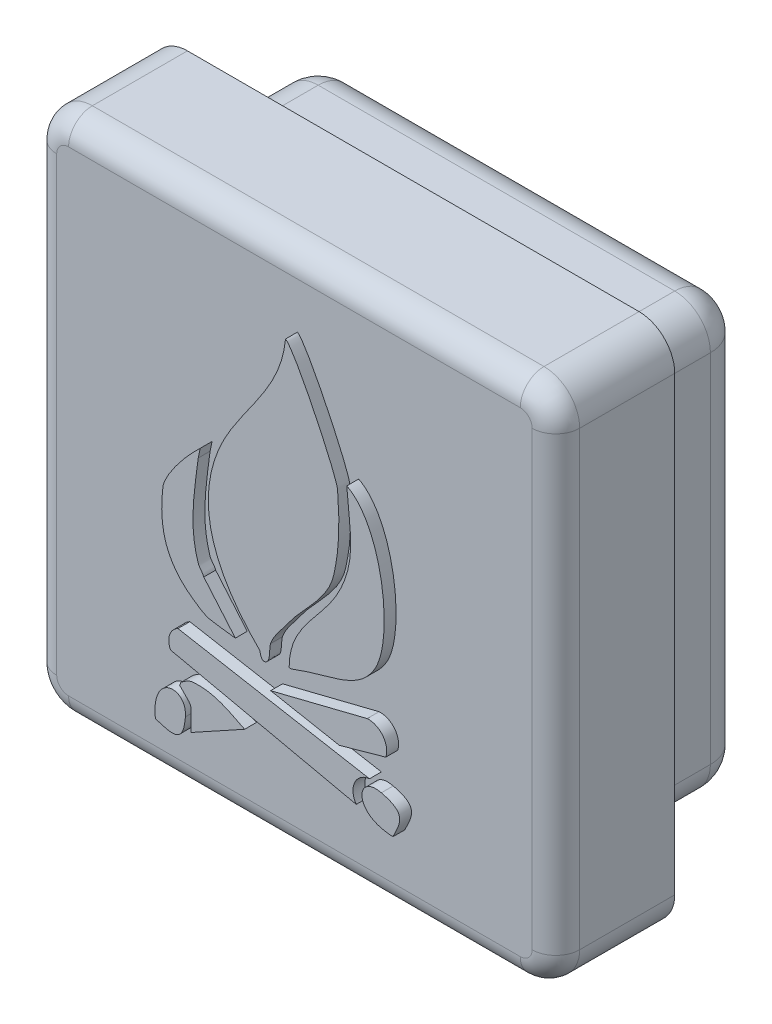
SolidWorks part; units mm, degrees
ref_plane "Plan de face" through (0, 0, 0) normal (0, 0, 1) x (1, 0, 0)
ref_plane "Plan de dessus" through (0, 0, 0) normal (0, 1, 0) x (1, 0, 0)
ref_plane "Plan de droite" through (0, 0, 0) normal (1, 0, 0) x (0, 0, -1)
sketch "Esquisse2" plane through (0, 0, 0) normal (0, 0, 1) x (1, 0, 0)
  line L1 (0, 0) -> (44, 0)
  line L2 (0, 0) -> (0, 44)
  line L3 (0, 44) -> (44, 44)
  line L4 (44, 0) -> (44, 44)
  dimension "D1" = 44
extrude "Boss.-Extru.1" add sketch "Esquisse2" along normal blind 10
sketch "Esquisse3" plane through (0, 0, 0) normal (0, 0, -1) x (-1, 0, 0)
  line L0 (-44, 44) -> (0, 44) construction
  line L1 (-40, 4) -> (-4, 4)
  line L2 (-40, 4) -> (-40, 40)
  line L3 (-40, 40) -> (-4, 40)
  line L4 (-4, 4) -> (-4, 40)
  line L5 (0, 44) -> (0, 0) construction
  dimension "D1" = 36
  dimension "D2" = 36
  dimension "D3" = 4
  dimension "D4" = 4
extrude "Boss.-Extru.2" add sketch "Esquisse3" along normal blind 10
sketch "Esquisse4" plane through (0, 0, 0) normal (0, 0, -1) x (-1, 0, 0)
  line L0 (-42.5, 42.5) -> (0, 42.5)
  line L1 (-40, 40) -> (-4, 40)
  line L2 (-40, 40) -> (-40, 4)
  line L3 (-40, 4) -> (-4, 4)
  line L4 (-4, 40) -> (-4, 4)
  line L8 (0, 44) -> (0, 0) construction
  line L9 (0, 42.5) -> (0, 0)
  line L11 (0, 0) -> (-42.5, 0)
  line L12 (0, 0) -> (-44, 0) construction
  line L15 (-42.5, 0) -> (-42.5, 42.5)
  line L16 (-44, 44) -> (0, 44) construction
  line L17 (-44, 0) -> (-44, 44) construction
  dimension "D1" = 1.5
  dimension "D2" = 1.5
extrude "Enlèv. mat.-Extru.1" cut sketch "Esquisse4" against normal blind 5
fillet "Congé1" radius 3 13 edges at (22, 40, -10) (4, 22, -10) (22, 4, -10) (40, 22, -10) (44, 0, 5) (44, 44, 5) (0, 0, 7.5) (0, 44, 5) (4, 4, -2.5) (4, 40, -2.5) (40, 4, -2.5) (40, 40, -2.5) (42.5, 42.5, 2.5)
fillet "Congé2" radius 2 8 edges at (0.8787, 0.8787, 10) (0, 22, 10) (0.8787, 43.1213, 10) (22, 44, 10) (43.1213, 43.1213, 10) (44, 22, 10) (43.1213, 0.8787, 10) (22, 0, 10)
sketch "Esquisse7" plane through (0, 0, 10) normal (0, 0, 1) x (1, 0, 0)
  line L0 (15.3741, 17.3468) -> (18.0303, 14.2218)
  line L1 (30.6866, 11.8781) -> (26.7803, 10.7843)
  line L2 (26.7803, 10.7843) -> (20.9991, 11.8781)
  line L3 (20.9991, 11.8781) -> (29.1241, 13.9093)
  line L4 (18.8116, 7.9718) -> (14.2803, 5.4718)
  line L5 (13.2006, 12.5063) -> (29.3172, 9.6184)
  line L7 (28.2006, 7.1938) -> (12.5756, 10.6313)
  line L9 (14.4366, 25.9406) -> (15.0694, 26.5734)
  line L10 (15.0694, 26.5734) -> (14.9053, 25.7843)
  arc A0 (29.1241, 13.9093) -> (30.6866, 11.8781) centre (29.2193, 12.366) cw
  arc A2 (12.5756, 10.6313) -> (13.2006, 12.5063) centre (13.8256, 11.2563) cw
  arc A3 (29.3172, 9.6184) -> (28.2006, 7.1938) centre (29.4761, 8.0758) ccw
  spline S0 degree 3 poles (14.9053, 25.7843) (14.5904, 23.2651) (14.0913, 20.5702) (14.9053, 18.1281) (15.0014, 17.84) (15.2781, 17.635) (15.3741, 17.3468) knots 0 0 0 0 1 1 1 2 2 2 2
  spline S1 degree 3 poles (18.0303, 14.2218) (17.3012, 14.326) (16.5651, 14.3899) (15.8428, 14.5343) (15.423, 14.6183) (14.8381, 15.0288) (14.4366, 15.3156) (12.0497, 17.0205) (11.5958, 19.2938) (11.9366, 22.1906) (12.0542, 23.1898) (13.6924, 25.1964) (14.4366, 25.9406) knots 0 0 0 0 1 1 1 2 2 2 3 3 3 4 4 4 4
  spline S2 degree 3 poles (20.9991, 15.3156) (20.8271, 14.7997) (21.0462, 13.925) (20.5303, 13.7531) (20.1531, 13.6274) (20.1379, 14.3018) (20.0616, 14.3781) (16.5677, 17.872) (14.6135, 21.9332) (16.4678, 26.8781) (17.9717, 30.8884) (21.8464, 33.6987) (22.2491, 38.1281) knots 4 4 4 4 5 5 5 6 6 6 7 7 7 8 8 8 8
  spline S3 degree 3 poles (22.2491, 38.1281) (23.0247, 37.7403) (26.55, 30.317) (26.6241, 29.3781) (26.8247, 26.8369) (26.7937, 25.1415) (26.3116, 22.9718) (25.8437, 20.8661) (23.7633, 19.3417) (22.5616, 17.6593) (22.0936, 17.0042) (21.2572, 16.0898) (20.9991, 15.3156) knots 0 0 0 0 1 1 1 2 2 2 3 3 3 4 4 4 4
  spline S4 degree 3 poles (22.8741, 14.3781) (22.7769, 14.3407) (22.5616, 14.2739) (22.5616, 14.3781) (22.5616, 17.7246) (25.3852, 19.244) (26.7803, 22.0343) (28.2695, 25.0127) (27.6271, 26.8984) (27.4053, 30.0031) knots 3 3 3 3 4 4 4 5 5 5 6 6 6 6
  spline S5 degree 3 poles (27.4053, 30.0031) (30.4392, 28.4861) (31.4108, 20.5851) (29.7491, 17.8156) (28.5783, 15.8642) (26.7183, 15.5866) (24.7491, 15.0031) (24.1174, 14.8159) (23.489, 14.6146) (22.8741, 14.3781) knots 0 0 0 0 1 1 1 2 2 2 3 3 3 3
  spline S6 degree 3 poles (13.8256, 6.3836) (13.6649, 4.2944) (12.8351, 4.4911) (11.3077, 4.9834) knots 1 1 1 1 2 2 2 2
  spline S7 degree 3 poles (11.3077, 4.9834) (10.8882, 8.4435) (13.9957, 8.5946) (13.8256, 6.3836) knots 0 0 0 0 1 1 1 1
  spline S8 degree 3 poles (13.3428, 8.4406) (13.3949, 8.5448) (13.4043, 8.6854) (13.4991, 8.7531) (13.7834, 8.9562) (14.0891, 9.1853) (14.4366, 9.2218) (16.1347, 9.4006) (17.3848, 8.6852) (18.8116, 7.9718) knots 0 0 0 0 1 1 1 2 2 2 3 3 3 3
  spline S9 degree 3 poles (14.2803, 5.4718) (14.2803, 7.7728) (14.5937, 7.1897) (13.3428, 8.4406) knots 0 0 0 0 1 1 1 1
  spline S10 degree 3 poles (30.313, 9.0938) (32.3492, 8.5995) (32.0217, 7.8121) (31.2904, 6.3836) knots 1 1 1 1 2 2 2 2
  spline S11 degree 3 poles (31.2904, 6.3836) (27.8079, 6.5256) (28.158, 9.6169) (30.313, 9.0938) knots 0 0 0 0 1 1 1 1
extrude "Boss.-Extru.4" add sketch "Esquisse7" along normal blind 1
